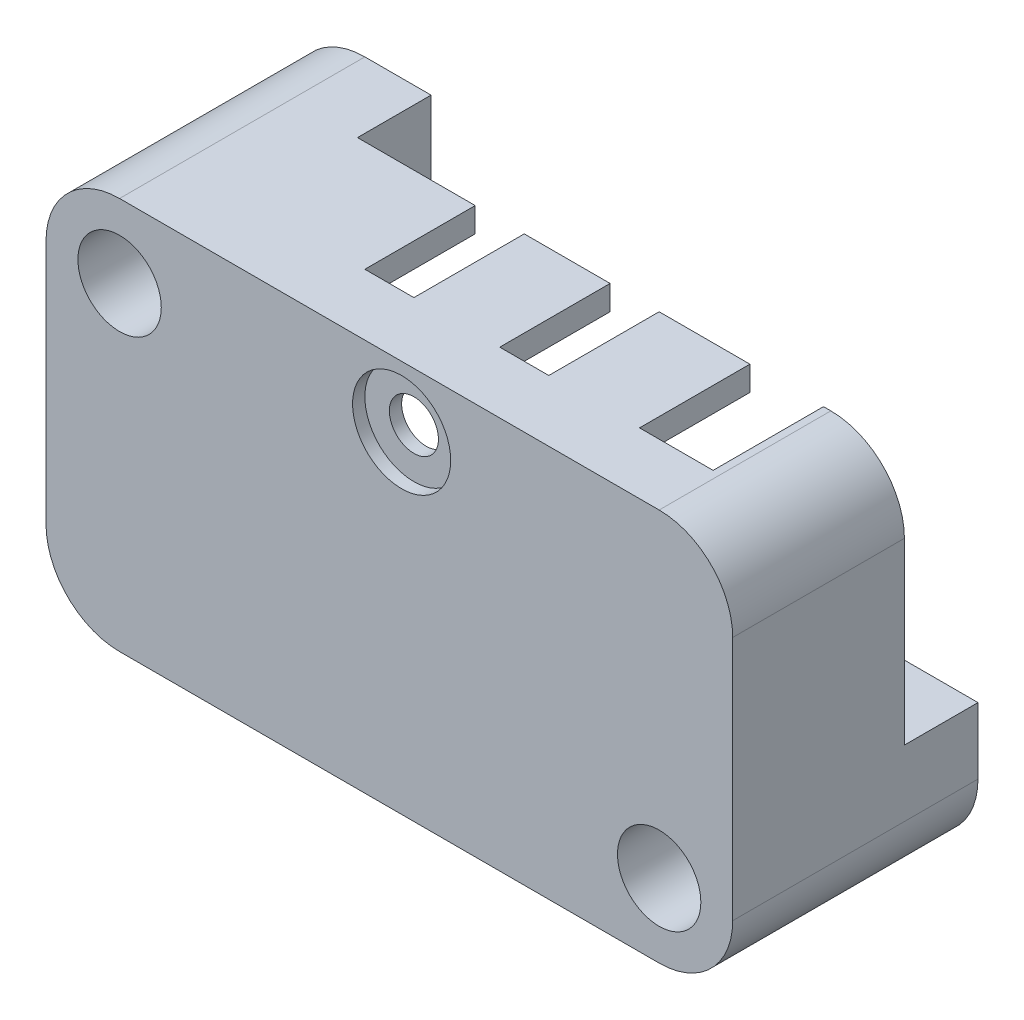
SolidWorks part; units mm, degrees
material "PA Typ 6"
ref_plane "Płaszczyzna przednia" through (0, 0, 0) normal (0, 0, 1) x (1, 0, 0)
ref_plane "Płaszczyzna górna" through (0, 0, 0) normal (0, 1, 0) x (1, 0, 0)
ref_plane "Płaszczyzna prawa" through (0, 0, 0) normal (1, 0, 0) x (0, 0, -1)
sketch "Szkic1" plane through (0, 0, 0) normal (0, 0, 1) x (1, 0, 0)
  line L1 (-14, -8) -> (14, -8)
  line L2 (-14, -8) -> (-14, 8)
  line L3 (-14, 8) -> (14, 8)
  line L4 (14, -8) -> (14, 8)
  line L5 (-14, -8) -> (14, 8) construction
  line L6 (-14, 8) -> (14, -8) construction
  point P0 (0, 0)
  dimension "D1" = 28
  dimension "D2" = 16
extrude "Dodanie-wyciągnięcie1" add sketch "Szkic1" along normal blind 10
sketch "Szkic2" plane through (0, 0, 10) normal (0, 0, 1) x (1, 0, 0)
  line L0 (14, 8) -> (-14, 8) construction
  line L1 (-14, -8) -> (14, -8) construction
  line L2 (14, -8) -> (14, 8) construction
  line L3 (-14, 8) -> (-14, -8) construction
  circle A0 centre (-11, 5) radius 1.7
  circle A1 centre (11, -5) radius 1.7
  dimension "D1" = 3.4
  dimension "D3" = 3
  dimension "D4" = 3
  dimension "D5" = 3
  dimension "D2" = 3
extrude "Wytnij-wyciągnięcie1" cut sketch "Szkic2" against normal up to next
fillet "Zaokrąglenie1" radius 3 4 edges at (-14, -8, 5) (14, -8, 5) (14, 8, 5) (-14, 8, 5)
ref_plane "Płaszczyzna1" through (0, 0, 5) normal (0, 0, 1) x (1, 0, 0)
sketch "Szkic3" plane through (0, 0, 5) normal (0, 0, 1) x (1, 0, 0)
  line L20 (11, 7) -> (-11, 7)
  line L21 (11, 7) -> (-7.3, 7)
  line L23 (-13, 5) -> (-13, -5)
  line L24 (-13, 1.3) -> (-13, -5)
  line L26 (-11, -7) -> (11, -7)
  line L27 (-11, -7) -> (7.3, -7)
  line L28 (-8.3, 5) -> (-8.3, 6)
  line L29 (13, -5) -> (13, 5)
  line L30 (13, -1.3) -> (13, 5)
  line L31 (-11, 2.3) -> (-12, 2.3)
  line L32 (8.3, -5) -> (8.3, -6)
  line L33 (11, -2.3) -> (12, -2.3)
  circle A5 centre (-11, 5) radius 2.7
  arc A6 (-11, 2.3) -> (-8.3, 5) centre (-11, 5) ccw
  circle A8 centre (11, -5) radius 2.7
  arc A9 (11, -2.3) -> (8.3, -5) centre (11, -5) ccw
  arc A14 (13, 5) -> (11, 7) centre (11, 5) ccw
  arc A15 (13, 5) -> (11, 7) centre (11, 5) ccw
  arc A16 (12, -2.3) -> (13, -1.3) centre (12, -1.3) ccw
  arc A17 (-13, -5) -> (-11, -7) centre (-11, -5) ccw
  arc A18 (-13, -5) -> (-11, -7) centre (-11, -5) ccw
  arc A19 (8.3, -6) -> (7.3, -7) centre (7.3, -6) cw
  arc A20 (-12, 2.3) -> (-13, 1.3) centre (-12, 1.3) ccw
  arc A21 (-7.3, 7) -> (-8.3, 6) centre (-7.3, 6) ccw
  dimension "D9" = 1
  dimension "D1" = 1
  dimension "D2" = 1
  dimension "D3" = 1
  dimension "D4" = 1
  dimension "D5" = 1
  dimension "D6" = 1
  dimension "D7" = 1
  dimension "D8" = 1
extrude "Wytnij-wyciągnięcie2" cut sketch "Szkic3" against normal blind 4 and the other way blind 4
sketch "Szkic4" plane through (0, 0, 0) normal (0, 0, -1) x (-1, 0, 0)
  line L0 (-11, 8) -> (11, 8) construction
  line L1 (-14, -5) -> (-14, 5) construction
  line L2 (14, 5) -> (14, -5) construction
  line L3 (11, -8) -> (-11, -8) construction
  line L4 (-11, 8) -> (8.3, 8)
  line L5 (-14, -2.3) -> (-14, 5)
  line L6 (14, 2.3) -> (14, -5)
  line L7 (11, -8) -> (-8.3, -8)
  line L8 (-8.3, -5) -> (-8.3, -8)
  line L9 (-11, -2.3) -> (-14, -2.3)
  line L10 (8.3, 5) -> (8.3, 8)
  line L11 (11, 2.3) -> (14, 2.3)
  circle A9 centre (-11, -5) radius 2.7
  arc A10 (-8.3, -5) -> (-11, -2.3) centre (-11, -5) ccw
  arc A11 (-11, 8) -> (-14, 5) centre (-11, 5) ccw construction
  circle A12 centre (11, 5) radius 2.7
  arc A13 (8.3, 5) -> (11, 2.3) centre (11, 5) ccw
  arc A14 (11, -8) -> (14, -5) centre (11, -5) ccw construction
  arc A15 (-11, 8) -> (-14, 5) centre (-11, 5) ccw
  arc A16 (11, -8) -> (14, -5) centre (11, -5) ccw
  dimension "D1" = 1
  dimension "D2" = 1
extrude "Wytnij-wyciągnięcie3" cut sketch "Szkic4" against normal blind 3
sketch "Szkic5" plane through (0, 8, 0) normal (0, 1, 0) x (1, 0, 0)
  line L0 (-8.3, -3) -> (11, -3) construction
  line L1 (2, -3) -> (4, -3)
  line L2 (2, -3) -> (2, -7.5)
  line L3 (2, -7.5) -> (4, -7.5)
  line L4 (4, -3) -> (4, -7.5)
  line L5 (-14, -10) -> (-14, 0) construction
  line L6 (7.7, -3) -> (10.7, -3)
  line L7 (7.7, -3) -> (7.7, -7.5)
  line L8 (7.7, -7.5) -> (10.7, -7.5)
  line L9 (10.7, -3) -> (10.7, -7.5)
  line L10 (-3.5, -3) -> (-1.5, -3)
  line L11 (-3.5, -3) -> (-3.5, -7.5)
  line L12 (-3.5, -7.5) -> (-1.5, -7.5)
  line L13 (-1.5, -3) -> (-1.5, -7.5)
  dimension "D1" = 4.5
  dimension "D2" = 2
  dimension "D3" = 2
  dimension "D4" = 3
  dimension "D5" = 10.5
  dimension "D6" = 5.5
  dimension "D7" = 9.2
extrude "Wytnij-wyciągnięcie4" cut sketch "Szkic5" against normal up to next
sketch "Szkic6" plane through (0, 0, 10) normal (0, 0, 1) x (1, 0, 0)
  line L0 (11, 8) -> (-11, 8) construction
  line L1 (14, -5) -> (14, 5) construction
  circle A0 centre (0.5, 5.5) radius 2
  dimension "D1" = 4
  dimension "D2" = 2.5
  dimension "D3" = 13.5
extrude "Wytnij-wyciągnięcie5" cut sketch "Szkic6" against normal blind 0.5
sketch "Szkic7" plane through (0, 0, 9.5) normal (0, 0, 1) x (1, 0, 0)
  circle A0 centre (0.5, 5.5) radius 1
  dimension "D1" = 2
extrude "Wytnij-wyciągnięcie6" cut sketch "Szkic7" against normal up to next
sketch "Szkic8" plane through (-14, 0, 0) normal (-1, 0, 0) x (0, 0, 1)
  line L0 (3, -5) -> (3, 2.3) construction
  line L1 (3, 2.1) -> (8, 2.1)
  line L2 (3, 2.1) -> (3, 1.1)
  line L3 (3, 1.1) -> (8, 1.1)
  line L4 (8, 2.1) -> (8, 1.1)
  line L5 (3, 2.3) -> (0, 2.3) construction
  line L6 (3, -3.3) -> (8, -3.3)
  line L7 (3, -3.3) -> (3, -4.3)
  line L8 (3, -4.3) -> (8, -4.3)
  line L9 (8, -3.3) -> (8, -4.3)
  dimension "D1" = 1
  dimension "D2" = 5
  dimension "D3" = 0.2
  dimension "D4" = 4.4
extrude "Wytnij-wyciągnięcie7" cut sketch "Szkic8" against normal up to next
sketch "Szkic9" plane through (0, -8, 0) normal (0, -1, 0) x (1, 0, 0)
  line L0 (8.3, 3) -> (-11, 3) construction
  line L1 (-1.5, 3) -> (-2.5, 3)
  line L2 (-1.5, 3) -> (-1.5, 8)
  line L3 (-1.5, 8) -> (-2.5, 8)
  line L4 (-2.5, 3) -> (-2.5, 8)
  line L5 (-14, 3) -> (-14, 10) construction
  dimension "D1" = 1
  dimension "D2" = 5
  dimension "D3" = 11.5
extrude "Wytnij-wyciągnięcie8" cut sketch "Szkic9" against normal up to next
